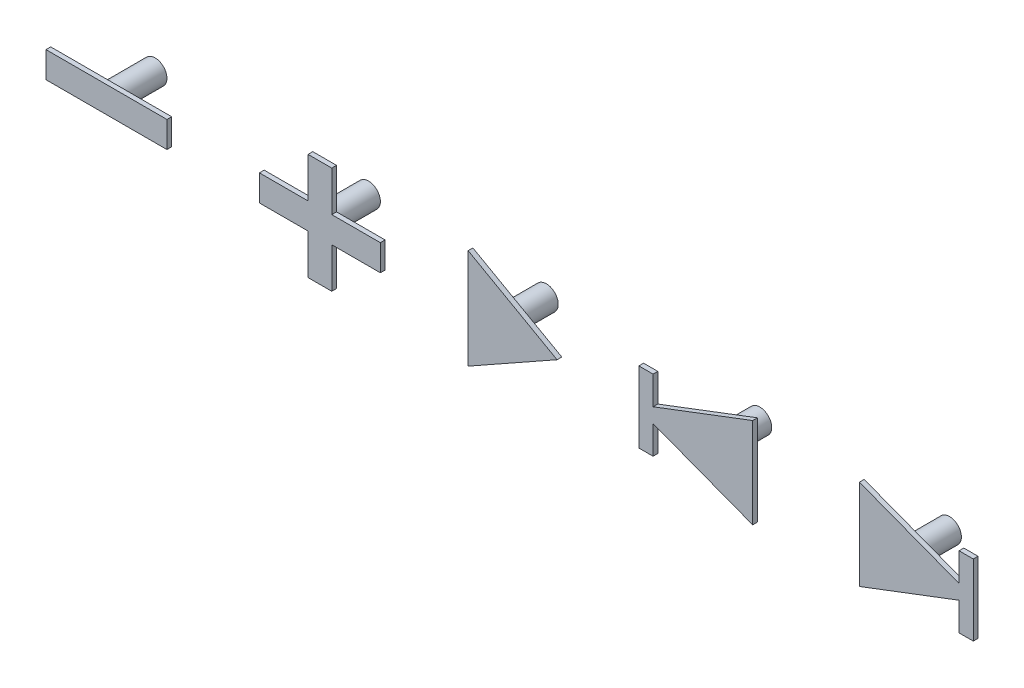
SolidWorks part; units mm, degrees
ref_plane "Front Plane" through (0, 0, 0) normal (0, 0, 1) x (1, 0, 0)
ref_plane "Top Plane" through (0, 0, 0) normal (0, 1, 0) x (1, 0, 0)
ref_plane "Right Plane" through (0, 0, 0) normal (1, 0, 0) x (0, 0, -1)
sketch "Sketch1" plane through (0, 0, 0) normal (0, 0, 1) x (1, 0, 0)
  line L1 (-61, 40) -> (61, 40)
  line L2 (-63, 38) -> (-63, -38)
  line L3 (-61, -40) -> (61, -40)
  line L4 (63, 38) -> (63, -38)
  line L5 (-63, 40) -> (63, -40) construction
  line L6 (-63, -40) -> (63, 40) construction
  arc A0 (61, 40) -> (63, 38) centre (61, 38) cw
  arc A1 (63, -38) -> (61, -40) centre (61, -38) cw
  arc A2 (-61, -40) -> (-63, -38) centre (-61, -38) cw
  arc A3 (-63, 38) -> (-61, 40) centre (-61, 38) cw
  point P0 (0, 0)
  dimension "D1" = 2
sketch "Sketch2" [suppressed] plane through (0, 0, 0) normal (0, 0, 1) x (1, 0, 0)
  line L0 (-5, 5.1169) -> (-5, -5.1169)
  line L1 (-4.2428, -5.5457) -> (4.2854, -0.4287)
  line L2 (4.2854, 0.4287) -> (-4.2428, 5.5457)
  line L3 (-10, -1.5) -> (-10, 1.5)
  line L4 (-10.5, 2) -> (-14, 2)
  line L5 (-14, 2) -> (-14, 5.5)
  line L6 (-14.5, 6) -> (-17.5, 6)
  line L7 (-18, 5.5) -> (-18, 2)
  line L8 (-18, 2) -> (-21.5, 2)
  line L9 (-22, 1.5) -> (-22, -1.5)
  line L10 (-21.5, -2) -> (-18, -2)
  line L11 (-18, -2) -> (-18, -5.5)
  line L12 (-17.5, -6) -> (-14.5, -6)
  line L13 (-14, -5.5) -> (-14, -2)
  line L14 (-14, -2) -> (-10.5, -2)
  line L15 (-28, 1.5) -> (-28, -1.5)
  line L16 (-28.5, -2) -> (-39.5, -2)
  line L17 (-40, -1.5) -> (-40, 1.5)
  line L18 (-39.5, 2) -> (-28.5, 2)
  line L19 (10, 4.5) -> (10, -4.5)
  line L20 (10.5, -5) -> (12.5, -5)
  line L21 (13, -4.5) -> (13, -2)
  line L22 (12.5, 5) -> (10.5, 5)
  line L23 (28, 5.2306) -> (28, -5.2306)
  line L24 (21.2969, 5.6875) -> (13, 2)
  line L25 (13, -2) -> (21.2969, -5.6875)
  line L26 (22, -5.2306) -> (22, 5.2306)
  line L27 (13, 2) -> (13, 4.5)
  line L28 (28.7031, -5.6875) -> (37, -2)
  line L29 (28.7031, 5.6875) -> (37, 2)
  line L30 (37, 2) -> (37, 4.5)
  line L31 (37.5, 5) -> (39.5, 5)
  line L32 (40, 4.5) -> (40, -4.5)
  line L33 (39.5, -5) -> (37.5, -5)
  line L34 (37, -4.5) -> (37, -2)
  arc A0 (-39.5, -2) -> (-40, -1.5) centre (-39.5, -1.5) cw
  arc A1 (-40, 1.5) -> (-39.5, 2) centre (-39.5, 1.5) cw
  arc A2 (-28.5, 2) -> (-28, 1.5) centre (-28.5, 1.5) cw
  arc A3 (-28, -1.5) -> (-28.5, -2) centre (-28.5, -1.5) cw
  arc A4 (-14.5, -6) -> (-14, -5.5) centre (-14.5, -5.5) ccw
  arc A5 (-17.5, -6) -> (-18, -5.5) centre (-17.5, -5.5) cw
  arc A6 (-21.5, -2) -> (-22, -1.5) centre (-21.5, -1.5) cw
  arc A7 (-22, 1.5) -> (-21.5, 2) centre (-21.5, 1.5) cw
  arc A8 (-18, 5.5) -> (-17.5, 6) centre (-17.5, 5.5) cw
  arc A9 (-14.5, 6) -> (-14, 5.5) centre (-14.5, 5.5) cw
  arc A10 (-10.5, 2) -> (-10, 1.5) centre (-10.5, 1.5) cw
  arc A11 (-10.5, -2) -> (-10, -1.5) centre (-10.5, -1.5) ccw
  arc A12 (-4.2428, -5.5457) -> (-5, -5.1169) centre (-4.5, -5.1169) cw
  arc A13 (-5, 5.1169) -> (-4.2428, 5.5457) centre (-4.5, 5.1169) cw
  arc A14 (4.2854, -0.4287) -> (4.2854, 0.4287) centre (4.0282, 0) ccw
  arc A15 (21.2969, 5.6875) -> (22, 5.2306) centre (21.5, 5.2306) cw
  arc A16 (22, -5.2306) -> (21.2969, -5.6875) centre (21.5, -5.2306) cw
  arc A17 (12.5, -5) -> (13, -4.5) centre (12.5, -4.5) ccw
  arc A18 (10.5, -5) -> (10, -4.5) centre (10.5, -4.5) cw
  arc A19 (10, 4.5) -> (10.5, 5) centre (10.5, 4.5) cw
  arc A20 (12.5, 5) -> (13, 4.5) centre (12.5, 4.5) cw
  arc A21 (28.7031, -5.6875) -> (28, -5.2306) centre (28.5, -5.2306) cw
  arc A22 (28, 5.2306) -> (28.7031, 5.6875) centre (28.5, 5.2306) cw
  arc A23 (37.5, -5) -> (37, -4.5) centre (37.5, -4.5) cw
  arc A24 (39.5, -5) -> (40, -4.5) centre (39.5, -4.5) ccw
  arc A25 (37, 4.5) -> (37.5, 5) centre (37.5, 4.5) cw
  arc A26 (40, 4.5) -> (39.5, 5) centre (39.5, 4.5) ccw
  dimension "D1" = 0.5
sketch "Sketch5" [suppressed] plane through (0, 0, 0) normal (0, 0, 1) x (1, 0, 0)
  line L0 (-21, 1) -> (-17, 1)
  line L1 (-39, 1) -> (-29, 1)
  line L2 (-39, 1) -> (-39, -1)
  line L3 (-39, -1) -> (-29, -1)
  line L4 (-29, 1) -> (-29, -1)
  line L5 (-17, 1) -> (-17, 5)
  line L6 (-17, 5) -> (-15, 5)
  line L7 (-15, 5) -> (-15, 1)
  line L8 (-15, 1) -> (-11, 1)
  line L9 (-11, 1) -> (-11, -1)
  line L10 (-11, -1) -> (-15, -1)
  line L11 (-15, -1) -> (-15, -5)
  line L12 (-15, -5) -> (-17, -5)
  line L13 (-17, -5) -> (-17, -1)
  line L14 (-17, -1) -> (-21, -1)
  line L15 (-21, -1) -> (-21, 1)
  line L16 (-4, 4) -> (-4, -4)
  line L17 (-4, -4) -> (3, 0)
  line L18 (3, 0) -> (-4, 4)
  line L19 (29, 4) -> (29, -4)
  line L20 (29, -4) -> (39, 0)
  line L21 (39, 0) -> (29, 4)
  line L22 (11, 0) -> (21, -4)
  line L23 (21, -4) -> (21, 4)
  line L24 (21, 4) -> (11, 0)
sketch "Sketch15" plane through (0, 0, 0) normal (0, 0, 1) x (1, 0, 0)
  circle A0 centre (-52.5, -27.5) radius 1
  circle A1 centre (-52.5, 27.5) radius 1
  circle A2 centre (52.5, -27.5) radius 1
  circle A3 centre (52.5, 27.5) radius 1
  point P0 (0, 0)
sketch "Sketch18" plane through (0, 0, 0) normal (0, 0, 1) x (1, 0, 0)
  circle A0 centre (60, 37) radius 1
  circle A1 centre (60, -37) radius 1
  circle A2 centre (-60, -37) radius 1
  circle A3 centre (-60, 37) radius 1
  circle A4 centre (0, 37) radius 1
  circle A5 centre (0, -37) radius 1
  circle A6 centre (-60, 0) radius 1
  circle A7 centre (60, 0) radius 1
ref_plane "Plane1" through (0, 0, 5) normal (0, 0, 1) x (1, 0, 0)
sketch "Sketch19" plane through (0, 0, 5) normal (0, 0, 1) x (1, 0, 0)
  line L0 (-5, 5.7) -> (-5, -5.7)
  line L1 (-4.2428, -6.1287) -> (5.2572, -0.4287)
  line L2 (5.2572, 0.4287) -> (-4.2428, 6.1287)
  line L3 (-10, -1.5) -> (-10, 1.5)
  line L4 (-10.5, 2) -> (-14, 2)
  line L5 (-14, 2) -> (-14, 5.5)
  line L6 (-14.5, 6) -> (-17.5, 6)
  line L7 (-18, 5.5) -> (-18, 2)
  line L8 (-18, 2) -> (-21.5, 2)
  line L9 (-22, 1.5) -> (-22, -1.5)
  line L10 (-21.5, -2) -> (-18, -2)
  line L11 (-18, -2) -> (-18, -5.5)
  line L12 (-17.5, -6) -> (-14.5, -6)
  line L13 (-14, -5.5) -> (-14, -2)
  line L14 (-14, -2) -> (-10.5, -2)
  line L15 (-28, 1.5) -> (-28, -1.5)
  line L16 (-28.5, -2) -> (-39.5, -2)
  line L17 (-40, -1.5) -> (-40, 1.5)
  line L18 (-39.5, 2) -> (-28.5, 2)
  line L19 (10, 4.5) -> (10, -4.5)
  line L20 (10.5, -5) -> (12.5, -5)
  line L21 (13, -4.5) -> (13, -2)
  line L22 (12.5, 5) -> (10.5, 5)
  line L23 (28, 5.2306) -> (28, -5.2306)
  line L24 (21.2969, 5.6875) -> (13, 2)
  line L25 (13, -2) -> (21.2969, -5.6875)
  line L26 (22, -5.2306) -> (22, 5.2306)
  line L27 (13, 2) -> (13, 4.5)
  line L28 (28.7031, -5.6875) -> (37, -2)
  line L29 (28.7031, 5.6875) -> (37, 2)
  line L30 (37, 2) -> (37, 4.5)
  line L31 (37.5, 5) -> (39.5, 5)
  line L32 (40, 4.5) -> (40, -4.5)
  line L33 (39.5, -5) -> (37.5, -5)
  line L34 (37, -4.5) -> (37, -2)
  arc A0 (-39.5, -2) -> (-40, -1.5) centre (-39.5, -1.5) cw
  arc A1 (-40, 1.5) -> (-39.5, 2) centre (-39.5, 1.5) cw
  arc A2 (-28.5, 2) -> (-28, 1.5) centre (-28.5, 1.5) cw
  arc A3 (-28, -1.5) -> (-28.5, -2) centre (-28.5, -1.5) cw
  arc A4 (-14.5, -6) -> (-14, -5.5) centre (-14.5, -5.5) ccw
  arc A5 (-17.5, -6) -> (-18, -5.5) centre (-17.5, -5.5) cw
  arc A6 (-21.5, -2) -> (-22, -1.5) centre (-21.5, -1.5) cw
  arc A7 (-22, 1.5) -> (-21.5, 2) centre (-21.5, 1.5) cw
  arc A8 (-18, 5.5) -> (-17.5, 6) centre (-17.5, 5.5) cw
  arc A9 (-14.5, 6) -> (-14, 5.5) centre (-14.5, 5.5) cw
  arc A10 (-10.5, 2) -> (-10, 1.5) centre (-10.5, 1.5) cw
  arc A11 (-10.5, -2) -> (-10, -1.5) centre (-10.5, -1.5) ccw
  arc A12 (-4.2428, -6.1287) -> (-5, -5.7) centre (-4.5, -5.7) cw
  arc A13 (-5, 5.7) -> (-4.2428, 6.1287) centre (-4.5, 5.7) cw
  arc A14 (5.2572, -0.4287) -> (5.2572, 0.4287) centre (5, 0) ccw
  arc A15 (21.2969, 5.6875) -> (22, 5.2306) centre (21.5, 5.2306) cw
  arc A16 (22, -5.2306) -> (21.2969, -5.6875) centre (21.5, -5.2306) cw
  arc A17 (12.5, -5) -> (13, -4.5) centre (12.5, -4.5) ccw
  arc A18 (10.5, -5) -> (10, -4.5) centre (10.5, -4.5) cw
  arc A19 (10, 4.5) -> (10.5, 5) centre (10.5, 4.5) cw
  arc A20 (12.5, 5) -> (13, 4.5) centre (12.5, 4.5) cw
  arc A21 (28.7031, -5.6875) -> (28, -5.2306) centre (28.5, -5.2306) cw
  arc A22 (28, 5.2306) -> (28.7031, 5.6875) centre (28.5, 5.2306) cw
  arc A23 (37.5, -5) -> (37, -4.5) centre (37.5, -4.5) cw
  arc A24 (39.5, -5) -> (40, -4.5) centre (39.5, -4.5) ccw
  arc A25 (37, 4.5) -> (37.5, 5) centre (37.5, 4.5) cw
  arc A26 (40, 4.5) -> (39.5, 5) centre (39.5, 4.5) ccw
  dimension "D1" = 0.5
sketch "Sketch20" plane through (0, 0, 5) normal (0, 0, 1) x (1, 0, 0)
  line L35 (-3.5, 4.2188) -> (-3.5, -4.2188)
  line L36 (-3.5, -4.2188) -> (4, 0)
  line L37 (4, 0) -> (-3.5, 4.2188)
  line L38 (-10.9, -1.1) -> (-10.9, 1.1)
  line L39 (-10.9, 1.1) -> (-15, 1.1)
  line L40 (-15, 1.1) -> (-15, 4.5)
  line L41 (-15, 4.5) -> (-17, 4.5)
  line L42 (-17, 4.5) -> (-17, 1.1)
  line L43 (-17, 1.1) -> (-21.1, 1.1)
  line L44 (-21.1, 1.1) -> (-21.1, -1.1)
  line L45 (-21.1, -1.1) -> (-17, -1.1)
  line L46 (-17, -1.1) -> (-17, -4.5)
  line L47 (-17, -4.5) -> (-15, -4.5)
  line L48 (-15, -4.5) -> (-15, -1.1)
  line L49 (-15, -1.1) -> (-10.9, -1.1)
  line L50 (-28.9, 1.1) -> (-28.9, -1.1)
  line L51 (-28.9, -1.1) -> (-39.1, -1.1)
  line L52 (-39.1, -1.1) -> (-39.1, 1.1)
  line L53 (-39.1, 1.1) -> (-28.9, 1.1)
  line L54 (10.9, 3) -> (10.9, -3)
  line L55 (10.9, -3) -> (12.1, -3)
  line L56 (12.1, -3) -> (12.1, -0.6151)
  line L57 (12.1, -0.6151) -> (20.5, -3.8098)
  line L58 (20.5, -3.8098) -> (20.5, 3.8098)
  line L59 (20.5, 3.8098) -> (12.1, 0.6151)
  line L60 (12.1, 0.6151) -> (12.1, 3)
  line L61 (12.1, 3) -> (10.9, 3)
  line L62 (29.5, 3.8098) -> (29.5, -3.8098)
  line L63 (29.5, -3.8098) -> (37.9, -0.6151)
  line L64 (37.9, -3) -> (37.9, -0.6151)
  line L65 (39.1, -3) -> (37.9, -3)
  line L66 (39.1, 3) -> (39.1, -3)
  line L67 (37.9, 3) -> (39.1, 3)
  line L68 (37.9, 0.6151) -> (37.9, 3)
  line L69 (29.5, 3.8098) -> (37.9, 0.6151)
sketch "Sketch21" plane through (0, 0, 5) normal (0, 0, 1) x (1, 0, 0)
  circle A0 centre (-1, 0) radius 1
  circle A1 centre (-16, 0) radius 1
  circle A2 centre (-34, 0) radius 1
  circle A3 centre (17, 0) radius 1
  circle A4 centre (33, 0) radius 1
sketch "Sketch22" plane through (0, 0, 0) normal (0, 0, 1) x (1, 0, 0)
  circle A0 centre (-34, 0) radius 0.6
  circle A1 centre (-16, 0) radius 0.6
  circle A2 centre (-1, 0) radius 0.6
  circle A3 centre (17, 0) radius 0.6
  circle A4 centre (33, 0) radius 0.6
extrude "Boss-Extrude3" add sketch "Sketch20" along normal blind 0.1 and the other way blind 0.3
extrude "Boss-Extrude4" add sketch "Sketch21" against normal blind 4
